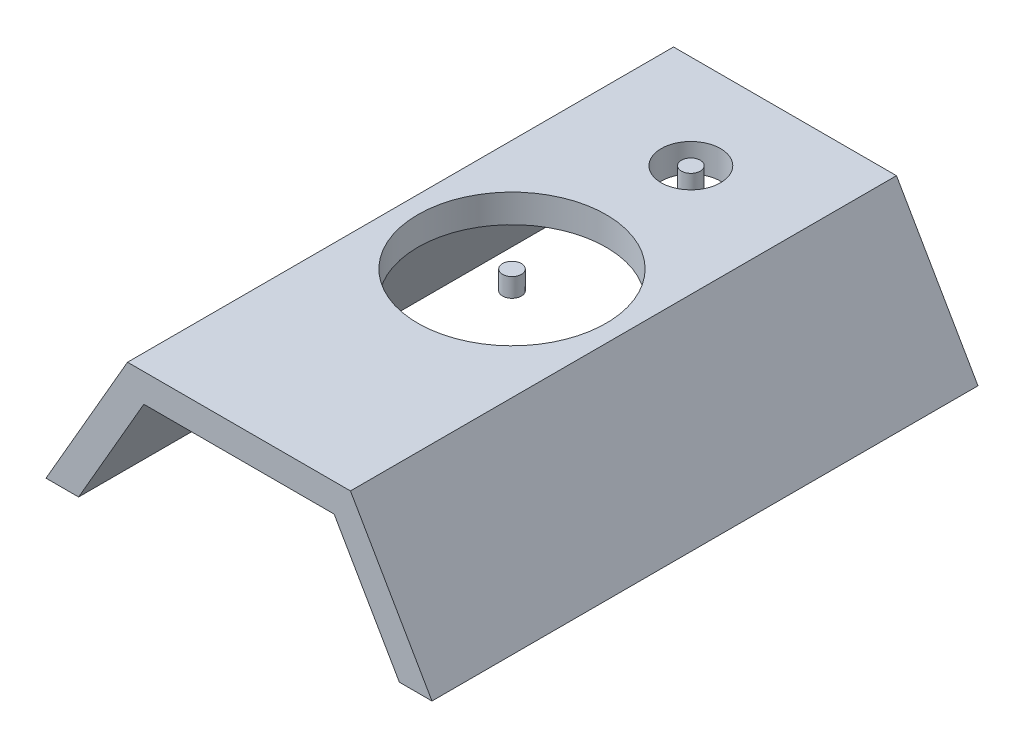
SolidWorks part; units mm, degrees
ref_plane "Plan de face" through (0, 0, 0) normal (0, 0, 1) x (1, 0, 0)
ref_plane "Plan de dessus" through (0, 0, 0) normal (0, 1, 0) x (1, 0, 0)
ref_plane "Plan de droite" through (0, 0, 0) normal (1, 0, 0) x (0, 0, -1)
sketch "Esquisse1" plane through (0, 0, 0) normal (0, 0, 1) x (1, 0, 0)
  line L0 (236.8076, 30) -> (219.4891, 0)
  line L1 (0, 30) -> (236.8076, 30)
  line L2 (0, 30) -> (0, 0)
  line L3 (0, 0) -> (236.8076, 0)
  line L4 (236.8076, 30) -> (236.8076, 0)
  line L5 (236.8076, 30) -> (254.1276, 0)
  line L6 (254.1276, 0) -> (236.8076, 0)
  line L7 (0, 30) -> (17.3185, 0)
  line L8 (17.3185, 0) -> (0, 30)
  line L9 (0, 30) -> (-17.3185, 0)
  line L10 (-17.3185, 0) -> (0, 0)
  line L11 (17.3185, 0) -> (0, -30)
  line L12 (-17.3185, 0) -> (0, -30)
  line L13 (0, -30) -> (-88.9889, -184.1513)
  line L14 (-17.3185, 0) -> (-86.5924, -120)
  line L15 (219.4891, 0) -> (236.8076, -30)
  line L16 (236.8076, -30) -> (254.1276, 0)
  line L17 (254.1276, 0) -> (323.4076, -120)
  line L18 (236.8076, -30) -> (326.5951, -185.5348)
  line L19 (323.4076, -120) -> (288.763, -120)
  line L20 (288.763, -120) -> (306.0907, -90.0053)
  line L21 (-86.5924, -120) -> (-51.9554, -120)
  line L22 (-51.9554, -120) -> (-69.2739, -90)
  line L23 (-69.2739, -90) -> (-34.637, -90)
  line L24 (306.0907, -90.0053) -> (271.4476, -90.0053)
  dimension "D1" = 30
  dimension "D3" = 34.64
  dimension "D4" = 17.3185
  dimension "D5" = 17.32
  dimension "D6" = 34.64
  dimension "D7" = 34.64
  dimension "D8" = 17.3185
  dimension "D9" = 17.3185
  dimension "D10" = 34.64
  dimension "D11" = 29.9974
  dimension "D12" = 34.64
  dimension "D13" = 34.6408
  dimension "D14" = 29.998
  dimension "D15" = 150
  dimension "D16" = 150
  dimension "D17" = 34.64
  dimension "D18" = 34.637
  dimension "D19" = 34.64
  dimension "D20" = 202.1707
  dimension "D21" = 410
  dimension "D22" = 410
  dimension "D23" = 236.8076
  dimension "D24" = 34.637
  dimension "D25" = 340.7185
extrude "Boss.-Extru.1" add sketch "Esquisse1" along normal blind 580 contours L22 L13 L12 L14 | L10 L12 L11 L3 | L9 L10 L2 | L7 L2 L3 | L1 L7 L3 L0 | L4 L0 L3 | L6 L5 L4 | L15 L16 L6 L3 | L18 L20 L17 L16 | L23 L22 L13 | L20 L24 L18 | L20 L19 L17 | L21 L22 L14
sketch "Esquisse2" plane through (0, 30, 0) normal (0, 1, 0) x (1, 0, 0)
  line L0 (236.8076, -580) -> (0, 0) construction
  line L1 (0, -580) -> (236.8076, 0) construction
  line L2 (118.4038, -290) -> (118.4038, 0) construction
  line L3 (0, 0) -> (236.8076, 0) construction
  line L4 (118.4038, 0) -> (118.4038, -100) construction
  circle A0 centre (118.4038, -290) radius 100
  circle A1 centre (118.4038, -100) radius 31.5
  dimension "D1" = 200
  dimension "D3" = 63
  dimension "D2" = 100
extrude "Enlèv. mat.-Extru.1" cut sketch "Esquisse2" against normal up to next
sketch "Esquisse4" plane through (0, 30, 0) normal (0, 1, 0) x (1, 0, 0)
  circle A0 centre (118.4038, -290) radius 10
  dimension "D1" = 20
extrude "Boss.-Extru.2" add sketch "Esquisse4" against normal blind 20 separate body
sketch "Esquisse5" plane through (0, 30, 0) normal (0, 1, 0) x (1, 0, 0)
  circle A0 centre (118.4038, -100) radius 10
  dimension "D1" = 20
extrude "Boss.-Extru.3" add sketch "Esquisse5" against normal blind 20 separate body
